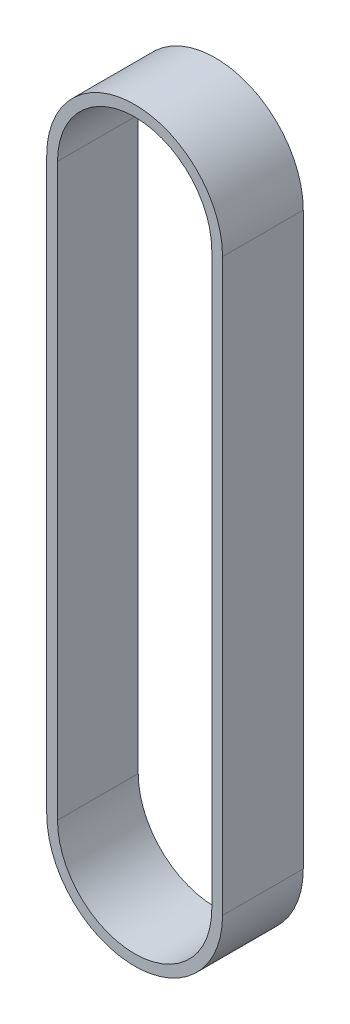
SolidWorks part; units mm, degrees
material "6061 合金"
ref_plane "前视基准面" through (0, 0, 0) normal (0, 0, 1) x (1, 0, 0)
ref_plane "上视基准面" through (0, 0, 0) normal (0, 1, 0) x (1, 0, 0)
ref_plane "右视基准面" through (0, 0, 0) normal (1, 0, 0) x (0, 0, -1)
sketch "草图1" plane through (0, 0, 0) normal (0, 0, 1) x (1, 0, 0)
  line L0 (0, -53) -> (0, 53) construction
  line L1 (-14.33, -53) -> (-14.33, 53)
  line L2 (14.33, -53) -> (14.33, 53)
  arc A0 (-14.33, -53) -> (14.33, -53) centre (0, -53) ccw
  arc A1 (14.33, 53) -> (-14.33, 53) centre (0, 53) ccw
  point P2 (0, 0)
  dimension "D1" = 14.33
  dimension "D2" = 106
extrude "拉伸-薄壁1" add sketch "草图1" along normal mid plane 15 thin thin type one direction wall 2
